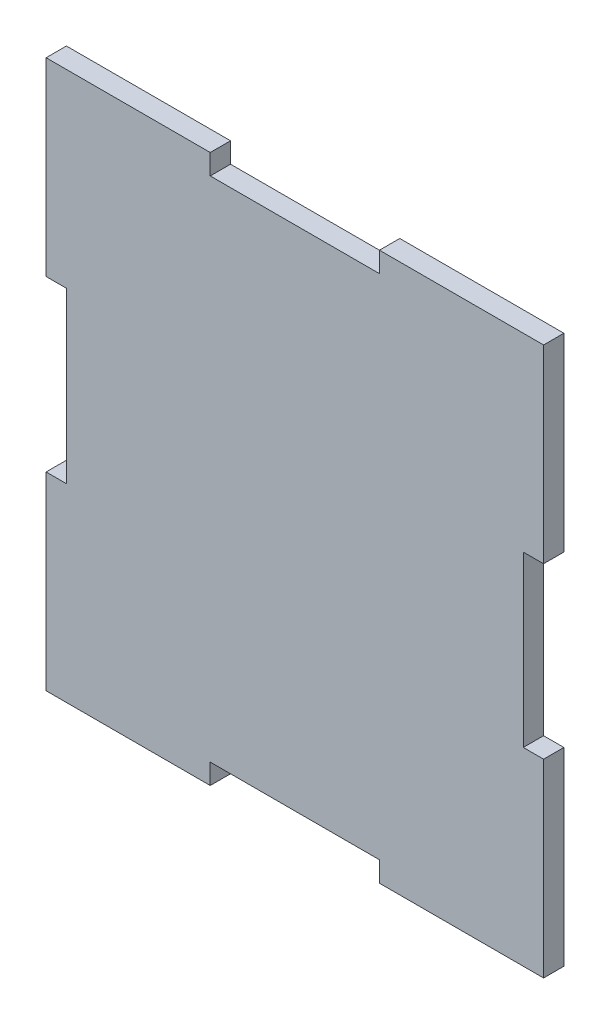
SolidWorks part; units mm, degrees
ref_plane "Alzado" through (0, 0, 0) normal (0, 0, 1) x (1, 0, 0)
ref_plane "Planta" through (0, 0, 0) normal (0, 1, 0) x (1, 0, 0)
ref_plane "Vista lateral" through (0, 0, 0) normal (1, 0, 0) x (0, 0, -1)
sketch "Croquis1" plane through (0, 0, 0) normal (0, 0, 1) x (1, 0, 0)
  line L0 (-73.5, 81) -> (-73.5, 25) construction
  line L1 (-73.5, 81) -> (-25, 81)
  line L2 (-73.5, 81) -> (-73.5, 25)
  line L3 (-73.5, -81) -> (-25, -81)
  line L4 (73.5, 81) -> (73.5, 25)
  line L5 (-73.5, 81) -> (73.5, -81) construction
  line L6 (-73.5, -81) -> (73.5, 81) construction
  line L8 (25, 81) -> (73.5, 81)
  line L9 (73.5, -25) -> (73.5, -81)
  line L10 (25, 81) -> (25, 75)
  line L11 (25, 75) -> (-25, 75)
  line L12 (-25, 81) -> (-25, 75)
  line L13 (73.5, 25) -> (67.5, 25)
  line L14 (25, -81) -> (73.5, -81)
  line L15 (73.5, -25) -> (67.5, -25)
  line L16 (67.5, 25) -> (67.5, -25)
  line L17 (-73.5, -25) -> (-73.5, -81)
  line L18 (25, -81) -> (25, -75)
  line L19 (25, -75) -> (-25, -75)
  line L20 (-25, -81) -> (-25, -75)
  line L21 (-73.5, -25) -> (-67.5, -25)
  line L23 (-73.5, 25) -> (-67.5, 25)
  line L24 (-67.5, -25) -> (-67.5, 25)
  point P0 (0, 0)
extrude "Saliente-Extruir1" add sketch "Croquis1" along normal blind 6 contours L24 L21 L2 L3 L20 L19 L18 L4 L15 L16 L13 L1 L10 L11 L12 L23
